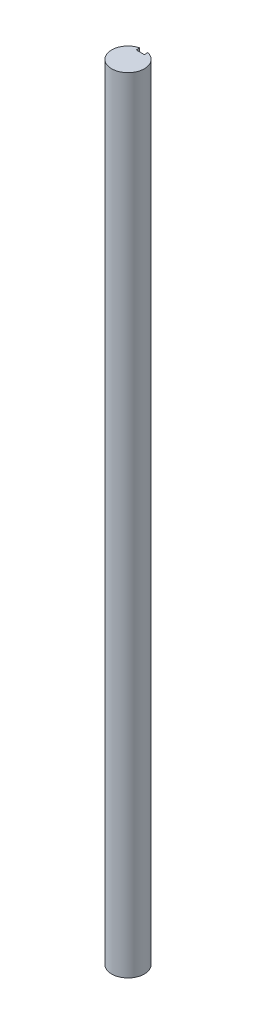
SolidWorks part; units mm, degrees
ref_plane "Front Plane" through (0, 0, 0) normal (0, 0, 1) x (1, 0, 0)
ref_plane "Top Plane" through (0, 0, 0) normal (0, 1, 0) x (1, 0, 0)
ref_plane "Right Plane" through (0, 0, 0) normal (1, 0, 0) x (0, 0, -1)
sketch "Sketch1" plane through (0, 0, 0) normal (0, 1, 0) x (1, 0, 0)
  line L0 (-1.5875, 6.1484) -> (-1.5875, 4.7625)
  line L1 (-1.5875, 4.7625) -> (1.5875, 4.7625)
  line L2 (1.5875, 4.7625) -> (1.5875, 6.1484)
  line L3 (0, 4.7625) -> (0, 0) construction
  arc A0 (-1.5875, 6.1484) -> (1.5875, 6.1484) centre (0, 0) ccw
  dimension "D1" = 12.7
  dimension "D2" = 4.7625
  dimension "D3" = 3.175
extrude "Extrude1" add sketch "Sketch1" along normal blind 304.8
